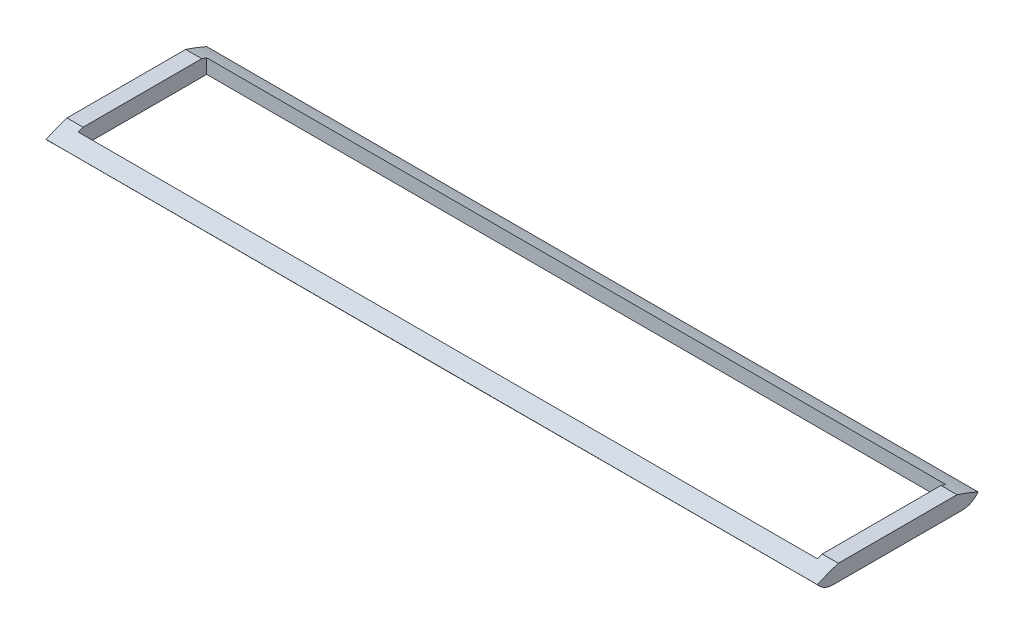
SolidWorks part; units mm, degrees
ref_plane "Front Plane" through (0, 0, 0) normal (0, 0, 1) x (1, 0, 0)
ref_plane "Top Plane" through (0, 0, 0) normal (0, 1, 0) x (1, 0, 0)
ref_plane "Right Plane" through (0, 0, 0) normal (1, 0, 0) x (0, 0, -1)
sketch "Sketch2" plane through (0, 0, 0) normal (0, 1, 0) x (1, 0, 0)
  line L0 (-146.05, 25.4) -> (146.05, 25.4)
  line L1 (-152.4, -31.75) -> (152.4, -31.75)
  line L2 (-152.4, -31.75) -> (-152.4, 31.75)
  line L3 (-152.4, 31.75) -> (152.4, 31.75)
  line L4 (152.4, -31.75) -> (152.4, 31.75)
  line L5 (-152.4, -31.75) -> (152.4, 31.75) construction
  line L6 (-152.4, 31.75) -> (152.4, -31.75) construction
  line L7 (146.05, -25.4) -> (146.05, 25.4)
  line L8 (-146.05, -25.4) -> (146.05, -25.4)
  line L9 (-146.05, -25.4) -> (-146.05, 25.4)
  point P0 (0, 0)
  dimension "D1" = 63.5
  dimension "D2" = 304.8
  dimension "D3" = 6.35
extrude "Boss-Extrude1" add sketch "Sketch2" along normal blind 6.35
sketch "Sketch3" plane through (152.4, 0, 0) normal (1, 0, 0) x (0, 0, -1)
  line L0 (-31.75, 6.35) -> (-31.75, 0) construction
  line L1 (31.75, 6.35) -> (31.75, 0) construction
  line L2 (-31.75, 0) -> (31.75, 0) construction
  line L3 (24.6995, 0) -> (31.1986, 0) construction
  line L4 (-31.75, 6.35) -> (31.75, 6.35) construction
  line L5 (-22.3566, 0) -> (-28.4632, 0) construction
  line L6 (-25.4, 0) -> (-25.4, -8.7364)
  line L7 (-25.4, -8.7364) -> (-38.7282, -8.7364)
  line L8 (-38.7282, -8.7364) -> (-38.7282, 15.542)
  line L9 (-38.7282, 15.542) -> (38.9235, 15.542)
  line L10 (38.9235, 15.542) -> (38.9235, -8.7364)
  line L11 (38.9235, -8.7364) -> (25.4, -8.7364)
  line L12 (25.4, -8.7364) -> (25.4, 0)
  spline S0 degree 2 poles (-31.75, 3.175) (0, 17.145) (31.75, 3.175) knots 0 0 0 1 1 1
  spline S1 degree 2 poles (-31.75, 3.175) (-29.2166, 0) (-25.4, 0) knots 0 0 0 1 1 1
  spline S2 degree 2 poles (31.75, 3.175) (29.4619, 0) (25.4, 0) knots 0 0 0 1 1 1
  dimension "D1" = 6.35
  dimension "D2" = 3.81
  dimension "D3" = 6.35
extrude "Cut-Extrude1" cut sketch "Sketch3" against normal through all
